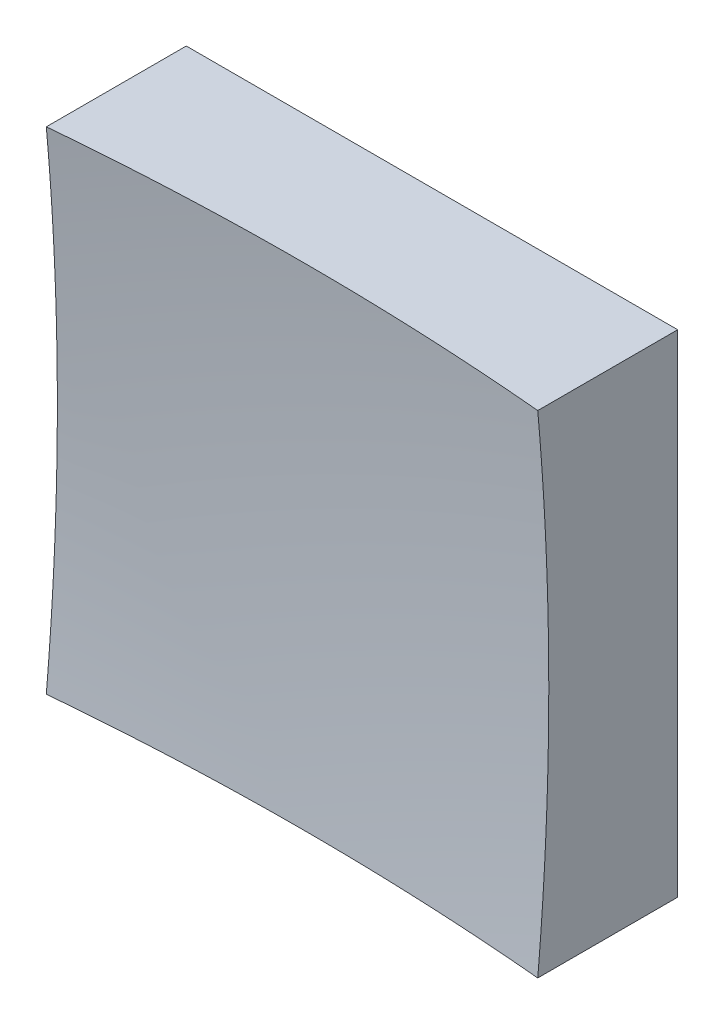
SolidWorks part; units mm, degrees
ref_plane "前视基准面" through (0, 0, 0) normal (0, 0, 1) x (1, 0, 0)
ref_plane "上视基准面" through (0, 0, 0) normal (0, 1, 0) x (1, 0, 0)
ref_plane "右视基准面" through (0, 0, 0) normal (1, 0, 0) x (0, 0, -1)
sketch "草图1" plane through (0, 0, 0) normal (0, 0, 1) x (1, 0, 0)
  line L1 (-6.25, 6.25) -> (6.25, 6.25)
  line L2 (-6.25, 6.25) -> (-6.25, -6.25)
  line L3 (-6.25, -6.25) -> (6.25, -6.25)
  line L4 (6.25, 6.25) -> (6.25, -6.25)
  line L5 (-6.25, 6.25) -> (6.25, -6.25) construction
  line L6 (-6.25, -6.25) -> (6.25, 6.25) construction
  point P0 (0, 0)
  dimension "D1" = 12.5
  dimension "D2" = 12.5
extrude "凸台-拉伸1" add sketch "草图1" along normal blind 10 contours L2 L3 L4 L1
sketch "草图2" plane through (0, 0, 0) normal (0, 1, 0) x (1, 0, 0)
  line L0 (-7.4603, -3) -> (7.3192, -3) construction
  line L1 (0, 0) -> (0, -12.1749) construction
  line L2 (68.2392, -57.3983) -> (0, -57.3983)
  line L3 (0, -57.3983) -> (0, -3)
  arc A1 (68.2392, -57.3983) -> (0, -3) centre (0, -73) ccw
  dimension "D2" = 140
  dimension "D1" = 3
revolve "切除-旋转2" cut sketch "草图2" angle 360 about L3
